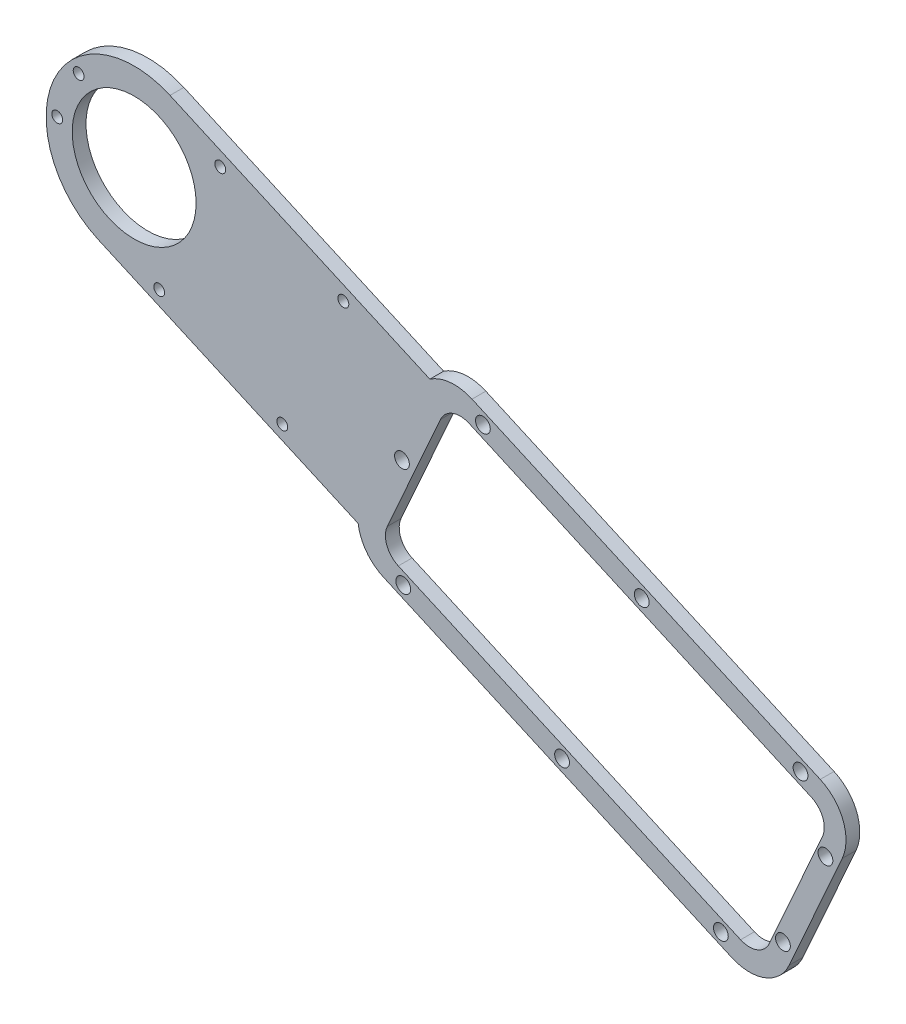
SolidWorks part; units mm, degrees
ref_plane "Front Plane" through (0, 0, 0) normal (0, 0, 1) x (1, 0, 0)
ref_plane "Top Plane" through (0, 0, 0) normal (0, 1, 0) x (1, 0, 0)
ref_plane "Right Plane" through (0, 0, 0) normal (1, 0, 0) x (0, 0, -1)
sketch "Sketch1" plane through (0, 0, 0) normal (0, 0, 1) x (1, 0, 0)
  line L0 (-81.4496, 53.8056) -> (-67.7738, 84.4844) construction
  line L1 (-91.6421, 47.2686) -> (-171.5223, 82.8771) construction
  line L2 (-75.2645, 89.2365) -> (-149.4221, 122.2941) construction
  line L3 (-72.7153, 90.8373) -> (-152.817, 126.5446)
  line L5 (-173.1746, 80.8766) -> (-93.0729, 45.1693)
  line L6 (-79.8678, 50.2314) -> (-67.6532, 77.6322)
  line L7 (-176.5357, 89.3012) -> (-161.0339, 124.0762) construction
  line L8 (-168.9326, 106.3571) -> (-73.7605, 63.9318) construction
  line L9 (-133.1238, 63.0229) -> (-112.7662, 108.691) construction
  line L10 (-162.5246, 125.6714) -> (-222.2994, 152.3174)
  line L11 (-73.7605, 63.9318) -> (-275.2251, 153.7395) construction
  line L12 (-179.0143, 88.6803) -> (-238.789, 115.3263)
  circle A0 centre (-230.5442, 133.8219) radius 14.25
  circle A2 centre (-95.5715, 49.0202) radius 1.7
  arc A3 (-152.817, 126.5446) -> (-162.5246, 125.6714) centre (-156.8885, 117.411) ccw
  arc A4 (-179.0143, 88.6803) -> (-173.1746, 80.8766) centre (-169.1031, 90.0102) ccw
  arc A5 (-93.0729, 45.1693) -> (-79.8678, 50.2314) centre (-89.0014, 54.3029) ccw
  arc A6 (-67.6532, 77.6322) -> (-72.7153, 90.8373) centre (-76.7868, 81.7037) ccw
  circle A7 centre (-132.1059, 65.3063) radius 1.7
  circle A8 centre (-168.6403, 81.5924) radius 1.7
  circle A9 centre (-150.3184, 122.6936) radius 1.7
  circle A10 centre (-113.784, 106.4076) radius 1.7
  circle A11 centre (-77.2496, 90.1215) radius 1.7
  circle A13 centre (-81.2951, 54.1522) radius 1.7
  circle A14 centre (-71.5234, 76.0729) radius 1.7
  circle A17 centre (-168.9326, 106.3571) radius 1.7
  arc A18 (-222.2994, 152.3174) -> (-238.789, 115.3263) centre (-230.5442, 133.8219) ccw
  dimension "D4" = 12
  dimension "D6" = 3.4
  dimension "D7" = 3.4
  dimension "D8" = 3.4
  dimension "D9" = 3.4
  dimension "D10" = 3.4
  dimension "D11" = 3.4
  dimension "D12" = 3.4
  dimension "D14" = 3.4
  dimension "D23" = 28.5
  dimension "D25" = 6
  dimension "D3" = 12
  dimension "D5" = 171.6559
  dimension "D1" = 2.5
  dimension "D2" = 2.5
  dimension "D15" = 0
  dimension "D16" = 0
  dimension "D17" = 40
  dimension "D18" = 40
  dimension "D20" = 40
  dimension "D21" = 40
extrude "Boss-Extrude1" add sketch "Sketch1" along normal blind 3.175
sketch "Sketch5" plane through (0, 0, 3.175) normal (0, 0, 1) x (1, 0, 0)
  line L0 (-181.3663, 93.0133) -> (-237.5676, 118.0664) construction
  line L1 (-238.789, 115.3263) -> (-179.0143, 88.6803) construction
  line L2 (-165.0202, 123.4993) -> (-223.5208, 149.5773) construction
  line L3 (-162.5246, 125.6714) -> (-222.2994, 152.3174) construction
  line L4 (-168.9326, 106.3571) -> (-249.0397, 142.0667) construction
  line L5 (-230.5442, 133.8219) -> (-248.2504, 135.0681) construction
  line L6 (-243.3069, 146.1579) -> (-230.5442, 133.8219) construction
  line L7 (-196.4664, 99.7446) -> (-182.4196, 131.2555) construction
  line L8 (-224.7805, 112.3663) -> (-210.7338, 143.8772) construction
  circle A0 centre (-230.5442, 133.8219) radius 17.25 construction
  arc A1 (-222.2994, 152.3174) -> (-238.789, 115.3263) centre (-230.5442, 133.8219) ccw construction
  circle A2 centre (-196.4664, 99.7446) radius 1.25
  circle A3 centre (-224.7805, 112.3663) radius 1.25
  circle A4 centre (-210.7338, 143.8772) radius 1.25
  circle A5 centre (-182.4196, 131.2555) radius 1.25
  circle A6 centre (-243.3069, 146.1579) radius 1.25
  circle A7 centre (-248.2504, 135.0681) radius 1.25
  circle A8 centre (-230.5442, 133.8219) radius 14.25 construction
  dimension "D1" = 3
  dimension "D4" = 2.5
  dimension "D5" = 2.5
  dimension "D6" = 2.5
  dimension "D7" = 2.5
  dimension "D8" = 20
  dimension "D9" = 2.5
  dimension "D10" = 20
  dimension "D11" = 2.5
  dimension "D12" = 14
  dimension "D14" = 17.75
  dimension "D15" = 17.75
  dimension "D2" = 3
  dimension "D3" = 3
  dimension "D13" = 45
extrude "Cut-Extrude4" cut sketch "Sketch5" against normal through all
sketch "Sketch6" plane through (0, 0, 3.175) normal (0, 0, 1) x (1, 0, 0)
  line L0 (-158.0596, 123.4073) -> (-70.1843, 84.2348)
  line L1 (-70.1843, 84.2348) -> (-86.4703, 47.7004)
  line L2 (-86.4703, 47.7004) -> (-174.3457, 86.8729)
  line L3 (-174.3457, 86.8729) -> (-158.0596, 123.4073)
  line L4 (-72.7153, 90.8373) -> (-152.817, 126.5446) construction
  line L5 (-173.1746, 80.8766) -> (-93.0729, 45.1693) construction
  line L6 (-79.8678, 50.2314) -> (-67.6532, 77.6322) construction
  dimension "D1" = 5
  dimension "D2" = 5
  dimension "D3" = 5
  dimension "D4" = 5
extrude "Cut-Extrude5" cut sketch "Sketch6" against normal blind 10
fillet "Fillet1" radius 5 2 edges at (-174.3457, 86.8729, 1.5875) (-158.0596, 123.4073, 1.5875)
fillet "Fillet2" radius 5 2 edges at (-86.4703, 47.7004, 1.5875) (-70.1843, 84.2348, 1.5875)
